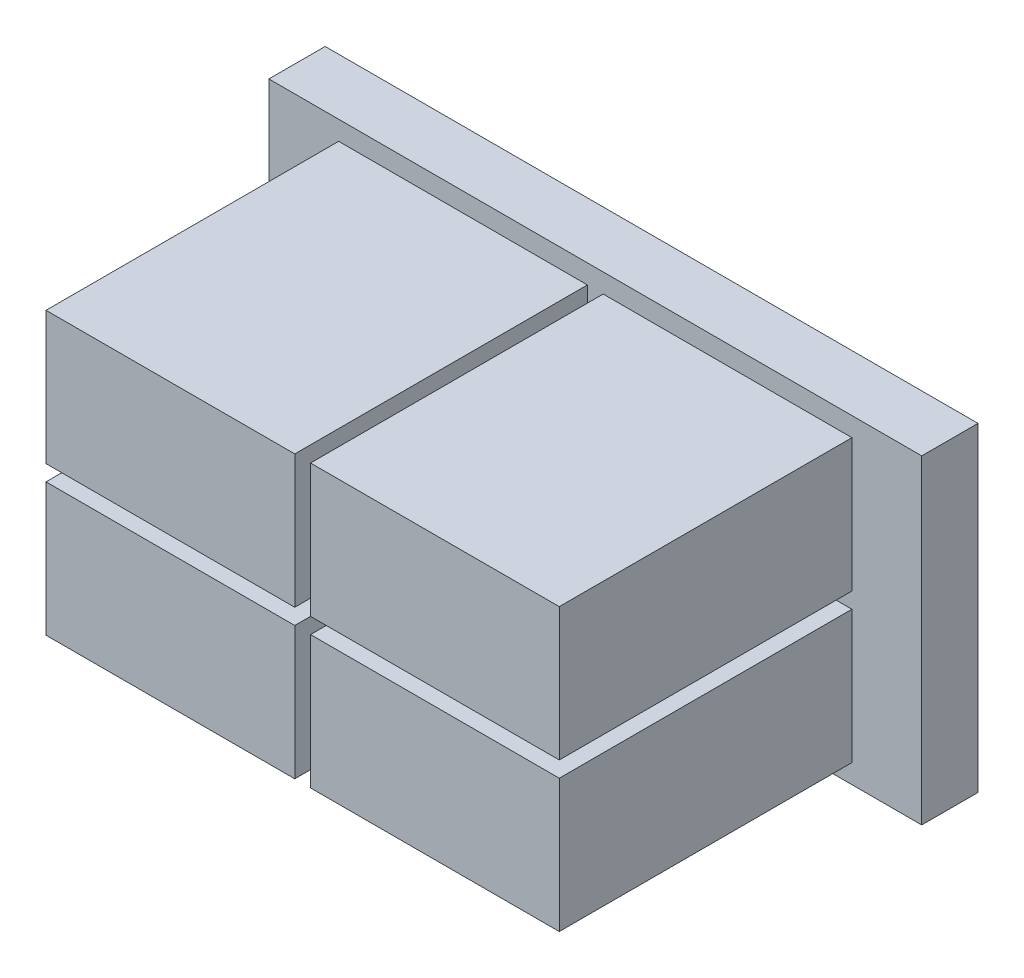
SolidWorks part; units mm, degrees
ref_plane "Alzado" through (0, 0, 0) normal (0, 0, 1) x (1, 0, 0)
ref_plane "Planta" through (0, 0, 0) normal (0, 1, 0) x (1, 0, 0)
ref_plane "Vista lateral" through (0, 0, 0) normal (1, 0, 0) x (0, 0, -1)
sketch "Croquis1" plane through (0, 0, 0) normal (0, 0, 1) x (1, 0, 0)
  line L1 (-14.5, 7.1) -> (14.5, 7.1)
  line L2 (-14.5, 7.1) -> (-14.5, -7.1)
  line L3 (-14.5, -7.1) -> (14.5, -7.1)
  line L4 (14.5, 7.1) -> (14.5, -7.1)
  line L5 (-14.5, 7.1) -> (14.5, -7.1) construction
  line L6 (-14.5, -7.1) -> (14.5, 7.1) construction
  point P0 (0, 0)
  dimension "D1" = 29
  dimension "D2" = 14.2
extrude "Saliente-Extruir1" add sketch "Croquis1" along normal blind 2.5
sketch "Croquis3" plane through (0, 0, 2.5) normal (0, 0, 1) x (1, 0, 0)
  line L0 (-11.4, 0.35) -> (-0.35, 0.35)
  line L1 (-11.4, 6.25) -> (-0.35, 6.25)
  line L2 (-11.4, 6.25) -> (-11.4, 0.35)
  line L3 (-11.4, -6.25) -> (-0.35, -6.25)
  line L4 (11.4, 6.25) -> (11.4, 0.35)
  line L5 (-11.4, 6.25) -> (11.4, -6.25) construction
  line L6 (-11.4, -6.25) -> (11.4, 6.25) construction
  line L7 (-11.4, -0.35) -> (-0.35, -0.35)
  line L8 (-0.35, 6.25) -> (-0.35, 0.35)
  line L9 (0.35, 6.25) -> (0.35, 0.35)
  line L10 (-11.4, -0.35) -> (-11.4, -6.25)
  line L11 (0.35, -6.25) -> (11.4, -6.25)
  line L12 (11.4, -0.35) -> (11.4, -6.25)
  line L13 (0.35, 6.25) -> (11.4, 6.25)
  line L14 (0.35, 0.35) -> (11.4, 0.35)
  line L15 (0.35, -0.35) -> (0.35, -6.25)
  line L16 (0.35, -0.35) -> (11.4, -0.35)
  line L17 (-0.35, -0.35) -> (-0.35, -6.25)
  point P0 (0, 0)
  dimension "D1" = 22.8
  dimension "D2" = 12.5
  dimension "D3" = 0.7
  dimension "D4" = 0.7
  dimension "D5" = 0.35
  dimension "D6" = 0.35
extrude "Saliente-Extruir2" add sketch "Croquis3" along normal blind 13
